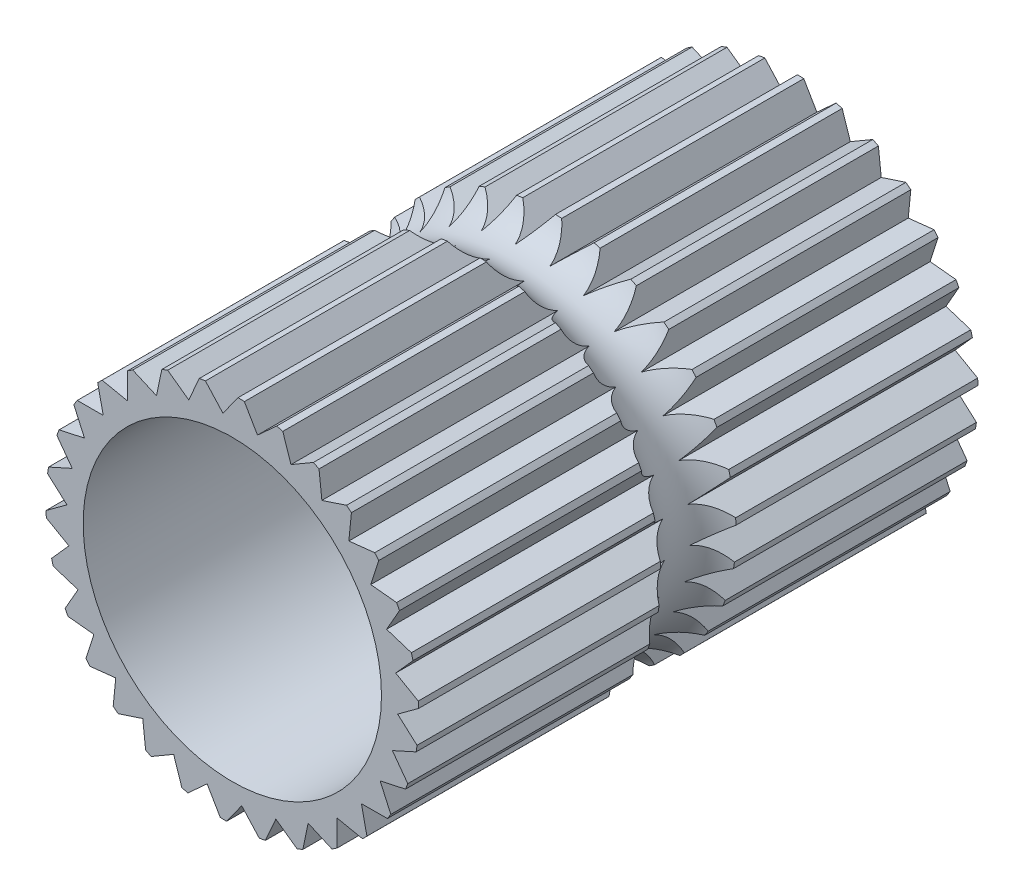
SolidWorks part; units mm, degrees
ref_plane "Front Plane" through (0, 0, 0) normal (0, 0, 1) x (1, 0, 0)
ref_plane "Top Plane" through (0, 0, 0) normal (0, 1, 0) x (1, 0, 0)
ref_plane "Right Plane" through (0, 0, 0) normal (1, 0, 0) x (0, 0, -1)
sketch "Sketch1" plane through (0, 0, 0) normal (0, 0, 1) x (1, 0, 0)
  circle A0 centre (0, 0) radius 2.5
  circle A1 centre (0, 0) radius 2
  dimension "D1" = 5
  dimension "D2" = 4
extrude "Boss-Extrude1" add sketch "Sketch1" along normal blind 7.5
ref_plane "Plane1" through (0, 0, 3.75) normal (0, 0, 1) x (1, 0, 0)
sketch "Sketch2" plane through (0, 0, 0) normal (0, 1, 0) x (1, 0, 0)
  line L0 (-2.75, -3.75) -> (2.75, -3.75) construction
  circle A0 centre (-0.1107, -3.75) radius 0.2755
sketch "Sketch4" plane through (0, 0, 3.75) normal (0, 0, 1) x (1, 0, 0)
  line L0 (0, 0) -> (0, -0.2452)
  line L1 (2, -2.2452) -> (3.1191, -2.2452)
  arc A0 (2, -2.2452) -> (0, -0.2452) centre (2, -0.2452) cw
  dimension "D1" = 2
sweep "Cut-Sweep1" cut profiles "Sketch2" path "Sketch4"
sketch "Sketch6" plane through (0, 0, 3.75) normal (0, 0, 1) x (1, 0, 0)
  circle A0 centre (0, 0) radius 2.5 construction
  circle A1 centre (0, 0) radius 2.5
sketch "Sketch7" plane through (0, 0, 0) normal (0, 1, 0) x (1, 0, 0)
  line L0 (-2.5, -3.75) -> (2.5, -3.75) construction
  circle A0 centre (2.7637, -3.75) radius 0.5698
sweep "Cut-Sweep2" cut profiles "Sketch7" path "Sketch6"
sketch "Sketch8" plane through (0, 0, 7.5) normal (0, 0, 1) x (1, 0, 0)
  line L0 (2.4227, 0.617) -> (2.1906, 0.3568)
  line L1 (2.1906, 0.3568) -> (2.4932, 0.1837)
  line L2 (2.2169, -0.1064) -> (2.477, -0.3387)
  line L3 (2.498, 0.0998) -> (2.2169, -0.1064)
  line L4 (2.1463, -0.565) -> (2.3524, -0.8463)
  line L5 (2.4642, -0.4217) -> (2.1463, -0.565)
  line L6 (1.982, -0.9989) -> (2.1251, -1.3169)
  line L7 (2.3226, -0.9248) -> (1.982, -0.9989)
  line L8 (1.731, -1.3892) -> (1.8048, -1.7299)
  line L9 (2.0796, -1.3875) -> (1.731, -1.3892)
  line L10 (1.4043, -1.7187) -> (1.4057, -2.0674)
  line L11 (1.7457, -1.7896) -> (1.4043, -1.7187)
  line L12 (1.0163, -1.9731) -> (0.9452, -2.3144)
  line L13 (1.3355, -2.1134) -> (1.0163, -1.9731)
  line L14 (0.5838, -2.1413) -> (0.4433, -2.4604)
  line L15 (0.8669, -2.3449) -> (0.5838, -2.1413)
  line L16 (0.1259, -2.2159) -> (-0.0779, -2.4988)
  line L17 (0.3604, -2.4739) -> (0.1259, -2.2159)
  line L18 (-0.3376, -2.1936) -> (-0.5957, -2.428)
  line L19 (-0.1618, -2.4948) -> (-0.3376, -2.1936)
  line L20 (-0.7863, -2.0755) -> (-1.0875, -2.2511)
  line L21 (-0.677, -2.4066) -> (-0.7863, -2.0755)
  line L22 (-1.2006, -1.8667) -> (-1.5318, -1.9758)
  line L23 (-1.1625, -2.2133) -> (-1.2006, -1.8667)
  line L24 (-1.5625, -1.5763) -> (-1.9091, -1.6141)
  line L25 (-1.5973, -1.9232) -> (-1.5625, -1.5763)
  line L26 (-1.8561, -1.217) -> (-2.203, -1.1819)
  line L27 (-1.9622, -1.5491) -> (-1.8561, -1.217)
  line L28 (-2.0685, -0.8045) -> (-2.4006, -0.6981)
  line L29 (-2.2414, -1.1072) -> (-2.0685, -0.8045)
  line L30 (-2.1906, -0.3568) -> (-2.4932, -0.1837)
  line L31 (-2.4227, -0.617) -> (-2.1906, -0.3568)
  line L32 (-2.2169, 0.1064) -> (-2.477, 0.3387)
  line L33 (-2.498, -0.0998) -> (-2.2169, 0.1064)
  line L34 (-2.1463, 0.565) -> (-2.3524, 0.8463)
  line L35 (-2.4642, 0.4217) -> (-2.1463, 0.565)
  line L36 (-1.982, 0.9989) -> (-2.1251, 1.3169)
  line L37 (-2.3226, 0.9248) -> (-1.982, 0.9989)
  line L38 (-1.731, 1.3892) -> (-1.8048, 1.7299)
  line L39 (-2.0796, 1.3875) -> (-1.731, 1.3892)
  line L40 (-1.4043, 1.7187) -> (-1.4057, 2.0674)
  line L41 (-1.7457, 1.7896) -> (-1.4043, 1.7187)
  line L42 (-1.0163, 1.9731) -> (-0.9452, 2.3144)
  line L43 (-1.3355, 2.1134) -> (-1.0163, 1.9731)
  line L44 (-0.5838, 2.1413) -> (-0.4433, 2.4604)
  line L45 (-0.8669, 2.3449) -> (-0.5838, 2.1413)
  line L46 (-0.1259, 2.2159) -> (0.0779, 2.4988)
  line L47 (-0.3604, 2.4739) -> (-0.1259, 2.2159)
  line L48 (0.3376, 2.1936) -> (0.5957, 2.428)
  line L49 (0.1618, 2.4948) -> (0.3376, 2.1936)
  line L50 (0.7863, 2.0755) -> (1.0875, 2.2511)
  line L51 (0.677, 2.4066) -> (0.7863, 2.0755)
  line L52 (1.2006, 1.8667) -> (1.5318, 1.9758)
  line L53 (1.1625, 2.2133) -> (1.2006, 1.8667)
  line L54 (1.5625, 1.5763) -> (1.9091, 1.6141)
  line L55 (1.5973, 1.9232) -> (1.5625, 1.5763)
  line L56 (1.8561, 1.217) -> (2.203, 1.1819)
  line L57 (1.9622, 1.5491) -> (1.8561, 1.217)
  line L58 (2.0685, 0.8045) -> (2.4006, 0.6981)
  line L59 (2.2414, 1.1072) -> (2.0685, 0.8045)
  circle A0 centre (0, 0) radius 2.5 construction
  arc A1 (2.4932, 0.1837) -> (2.4227, 0.617) centre (0, 0) ccw
  arc A2 (2.477, -0.3387) -> (2.498, 0.0998) centre (0, 0) ccw
  arc A3 (2.3524, -0.8463) -> (2.4642, -0.4217) centre (0, 0) ccw
  arc A4 (2.1251, -1.3169) -> (2.3226, -0.9248) centre (0, 0) ccw
  arc A5 (1.8048, -1.7299) -> (2.0796, -1.3875) centre (0, 0) ccw
  arc A6 (1.4057, -2.0674) -> (1.7457, -1.7896) centre (0, 0) ccw
  arc A7 (0.9452, -2.3144) -> (1.3355, -2.1134) centre (0, 0) ccw
  arc A8 (0.4433, -2.4604) -> (0.8669, -2.3449) centre (0, 0) ccw
  arc A9 (-0.0779, -2.4988) -> (0.3604, -2.4739) centre (0, 0) ccw
  arc A10 (-0.5957, -2.428) -> (-0.1618, -2.4948) centre (0, 0) ccw
  arc A11 (-1.0875, -2.2511) -> (-0.677, -2.4066) centre (0, 0) ccw
  arc A12 (-1.5318, -1.9758) -> (-1.1625, -2.2133) centre (0, 0) ccw
  arc A13 (-1.9091, -1.6141) -> (-1.5973, -1.9232) centre (0, 0) ccw
  arc A14 (-2.203, -1.1819) -> (-1.9622, -1.5491) centre (0, 0) ccw
  arc A15 (-2.4006, -0.6981) -> (-2.2414, -1.1072) centre (0, 0) ccw
  arc A16 (-2.4932, -0.1837) -> (-2.4227, -0.617) centre (0, 0) ccw
  arc A17 (-2.477, 0.3387) -> (-2.498, -0.0998) centre (0, 0) ccw
  arc A18 (-2.3524, 0.8463) -> (-2.4642, 0.4217) centre (0, 0) ccw
  arc A19 (-2.1251, 1.3169) -> (-2.3226, 0.9248) centre (0, 0) ccw
  arc A20 (-1.8048, 1.7299) -> (-2.0796, 1.3875) centre (0, 0) ccw
  arc A21 (-1.4057, 2.0674) -> (-1.7457, 1.7896) centre (0, 0) ccw
  arc A22 (-0.9452, 2.3144) -> (-1.3355, 2.1134) centre (0, 0) ccw
  arc A23 (-0.4433, 2.4604) -> (-0.8669, 2.3449) centre (0, 0) ccw
  arc A24 (0.0779, 2.4988) -> (-0.3604, 2.4739) centre (0, 0) ccw
  arc A25 (0.5957, 2.428) -> (0.1618, 2.4948) centre (0, 0) ccw
  arc A26 (1.0875, 2.2511) -> (0.677, 2.4066) centre (0, 0) ccw
  arc A27 (1.5318, 1.9758) -> (1.1625, 2.2133) centre (0, 0) ccw
  arc A28 (1.9091, 1.6141) -> (1.5973, 1.9232) centre (0, 0) ccw
  arc A29 (2.203, 1.1819) -> (1.9622, 1.5491) centre (0, 0) ccw
  arc A30 (2.4006, 0.6981) -> (2.2414, 1.1072) centre (0, 0) ccw
  point P79 (0, 0)
  dimension "D1" = 30
extrude "Cut-Extrude2" cut sketch "Sketch8" against normal blind 10
